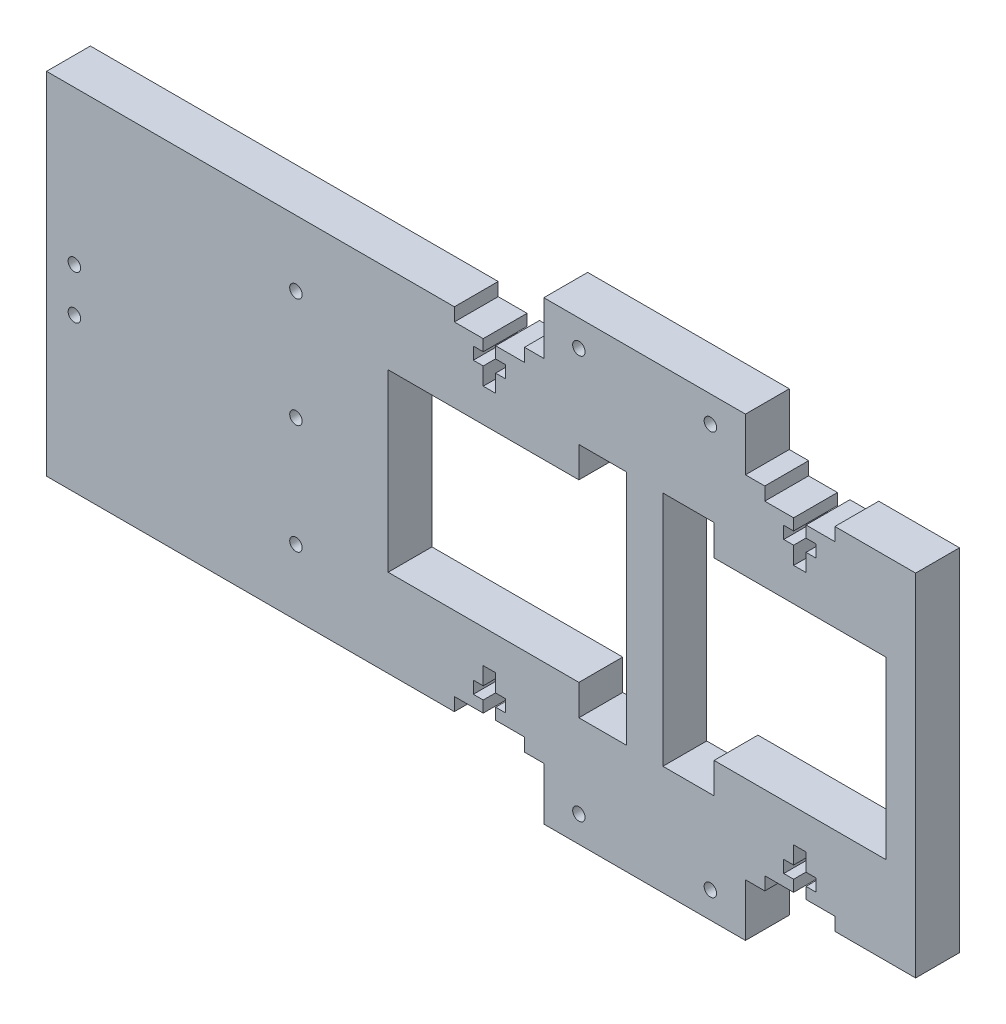
SolidWorks part; units mm, degrees
ref_plane "Front Plane" through (0, 0, 0) normal (0, 0, 1) x (1, 0, 0)
ref_plane "Top Plane" through (0, 0, 0) normal (0, 1, 0) x (1, 0, 0)
ref_plane "Right Plane" through (0, 0, 0) normal (1, 0, 0) x (0, 0, -1)
sketch "Sketch1" plane through (0, 0, 0) normal (0, 0, 1) x (1, 0, 0)
  line L0 (109, 80) -> (109, 77)
  line L1 (0, 0) -> (38.1871, 0)
  line L2 (143.4175, 20) -> (143.4175, 0)
  line L3 (5, 80) -> (38.1871, 80)
  line L4 (58.5936, 80) -> (58.5936, 92)
  line L5 (109, 77) -> (115.58, 77)
  line L6 (118.42, 71.6) -> (118.42, 67.6)
  line L7 (118.42, 77) -> (118.42, 74.4)
  line L8 (118.42, 67.6) -> (115.58, 67.6)
  line L9 (115.58, 71.6) -> (115.58, 67.6)
  line L10 (120.67, 71.6) -> (118.42, 71.6)
  line L11 (113.33, 74.4) -> (115.58, 74.4)
  line L12 (113.33, 74.4) -> (113.33, 71.6)
  line L13 (113.33, 71.6) -> (115.58, 71.6)
  line L14 (120.67, 74.4) -> (120.67, 71.6)
  line L15 (120.67, 74.4) -> (118.42, 74.4)
  line L16 (115.58, 77) -> (115.58, 74.4)
  line L17 (125, 77) -> (118.42, 77)
  line L18 (125, 80) -> (125, 77)
  line L19 (125, 80) -> (143.4175, 80)
  line L20 (247.4135, 40) -> (-51.1789, 40) construction
  line L21 (109, 0) -> (109, 3)
  line L22 (109, 3) -> (115.58, 3)
  line L23 (115.58, 3) -> (115.58, 5.6)
  line L24 (113.33, 5.6) -> (115.58, 5.6)
  line L25 (113.33, 5.6) -> (113.33, 8.4)
  line L26 (113.33, 8.4) -> (115.58, 8.4)
  line L27 (115.58, 8.4) -> (115.58, 12.4)
  line L28 (118.42, 12.4) -> (115.58, 12.4)
  line L29 (118.42, 8.4) -> (118.42, 12.4)
  line L30 (120.67, 8.4) -> (118.42, 8.4)
  line L31 (120.67, 5.6) -> (120.67, 8.4)
  line L32 (120.67, 5.6) -> (118.42, 5.6)
  line L33 (118.42, 3) -> (118.42, 5.6)
  line L34 (125, 3) -> (118.42, 3)
  line L35 (125, 0) -> (125, 3)
  line L36 (143.4175, 60) -> (143.4175, 80)
  line L37 (143.4175, 0) -> (125, 0)
  line L38 (58.5936, 92) -> (104.5936, 92)
  line L39 (104.5936, 92) -> (104.5936, 80)
  line L40 (58.5936, 0) -> (58.5936, -12)
  line L41 (58.5936, -12) -> (104.5936, -12)
  line L42 (104.5936, -12) -> (104.5936, 0)
  line L43 (104.5936, 80) -> (109, 80)
  line L44 (104.5936, 0) -> (109, 0)
  line L45 (5, 80) -> (-15.6021, 80)
  line L46 (136.6006, 60) -> (136.6006, 20)
  line L47 (-15.6021, 0) -> (0, 0)
  line L48 (81.5936, -22.2503) -> (81.5936, 103.8754) construction
  line L49 (54.1871, 0) -> (54.1871, 3)
  line L50 (54.1871, 3) -> (47.6071, 3)
  line L51 (44.7671, 12.4) -> (47.6071, 12.4)
  line L52 (47.6071, 8.4) -> (47.6071, 12.4)
  line L53 (49.8571, 8.4) -> (47.6071, 8.4)
  line L54 (49.8571, 5.6) -> (49.8571, 8.4)
  line L55 (49.8571, 5.6) -> (47.6071, 5.6)
  line L56 (47.6071, 3) -> (47.6071, 5.6)
  line L57 (38.1871, 0) -> (38.1871, 3)
  line L58 (38.1871, 3) -> (44.7671, 3)
  line L59 (44.7671, 3) -> (44.7671, 5.6)
  line L60 (42.5171, 5.6) -> (44.7671, 5.6)
  line L61 (42.5171, 5.6) -> (42.5171, 8.4)
  line L62 (42.5171, 8.4) -> (44.7671, 8.4)
  line L63 (44.7671, 8.4) -> (44.7671, 12.4)
  line L64 (58.5936, 80) -> (54.1871, 80)
  line L65 (54.1871, 80) -> (54.1871, 77)
  line L66 (54.1871, 77) -> (47.6071, 77)
  line L67 (49.8571, 71.6) -> (47.6071, 71.6)
  line L68 (49.8571, 74.4) -> (49.8571, 71.6)
  line L69 (49.8571, 74.4) -> (47.6071, 74.4)
  line L70 (47.6071, 77) -> (47.6071, 74.4)
  line L71 (38.1871, 80) -> (38.1871, 77)
  line L72 (38.1871, 77) -> (44.7671, 77)
  line L73 (44.7671, 77) -> (44.7671, 74.4)
  line L74 (42.5171, 74.4) -> (44.7671, 74.4)
  line L75 (42.5171, 74.4) -> (42.5171, 71.6)
  line L76 (42.5171, 71.6) -> (44.7671, 71.6)
  line L77 (47.6071, 71.6) -> (47.6071, 67.6)
  line L78 (44.7671, 67.6) -> (47.6071, 67.6)
  line L79 (44.7671, 71.6) -> (44.7671, 67.6)
  line L80 (23.079, 60) -> (66.5936, 60)
  line L81 (54.1871, 0) -> (58.5936, 0)
  line L82 (23.079, 60) -> (23.079, 20)
  line L83 (23.079, 20) -> (66.5936, 20)
  line L84 (97.4428, 60) -> (136.6006, 60)
  line L85 (66.5936, 67) -> (77.4275, 67)
  line L86 (66.5936, 67) -> (66.5936, 60)
  line L87 (66.5936, 13) -> (77.4275, 13)
  line L88 (97.4428, 67) -> (97.4428, 60)
  line L89 (97.4428, 20) -> (136.6006, 20)
  line L90 (97.4428, 20) -> (97.4428, 13)
  line L91 (66.5936, 20) -> (66.5936, 13)
  line L92 (85.7596, 67) -> (85.7596, 13)
  line L93 (143.4175, 60) -> (143.4175, 20)
  line L94 (-54.8538, 80) -> (-54.8538, 0)
  line L95 (-15.6021, 0) -> (-54.8538, 0)
  line L96 (77.4275, 67) -> (77.4275, 13)
  line L97 (-15.6021, 80) -> (-54.8538, 80)
  line L98 (85.7596, 67) -> (97.4428, 67)
  line L99 (85.7596, 13) -> (97.4428, 13)
  circle A0 centre (2.0378, 40) radius 1.42
  circle A1 centre (2.0378, 65) radius 1.42
  circle A2 centre (2.0378, 15) radius 1.42
  circle A3 centre (66.5936, 86) radius 1.42
  circle A4 centre (96.5936, 86) radius 1.42
  circle A5 centre (96.5936, -6) radius 1.42
  circle A6 centre (66.5936, -6) radius 1.42
  circle A7 centre (-48.5024, 45) radius 1.42
  circle A8 centre (-48.5024, 35) radius 1.42
  point P19 (117, 67.6)
  point P116 (38.1871, 78.5)
  point P117 (54.1871, 78.5)
  dimension "D3" = 2.84
  dimension "D6" = 2.84
  dimension "D7" = 2.84
  dimension "D11" = 54.8129
  dimension "D2" = 20
  dimension "D1" = 141.3798
  dimension "D14" = 4
  dimension "D9" = 2.84
  dimension "D16" = 2.84
  dimension "D17" = 2.84
  dimension "D4" = 25
  dimension "D5" = 25
  dimension "D8" = 20
  dimension "D10" = 36.1494
  dimension "D12" = 4
  dimension "D13" = 9.4
  dimension "D15" = 2.6
extrude "Boss-Extrude1" add sketch "Sketch1" along normal blind 10
